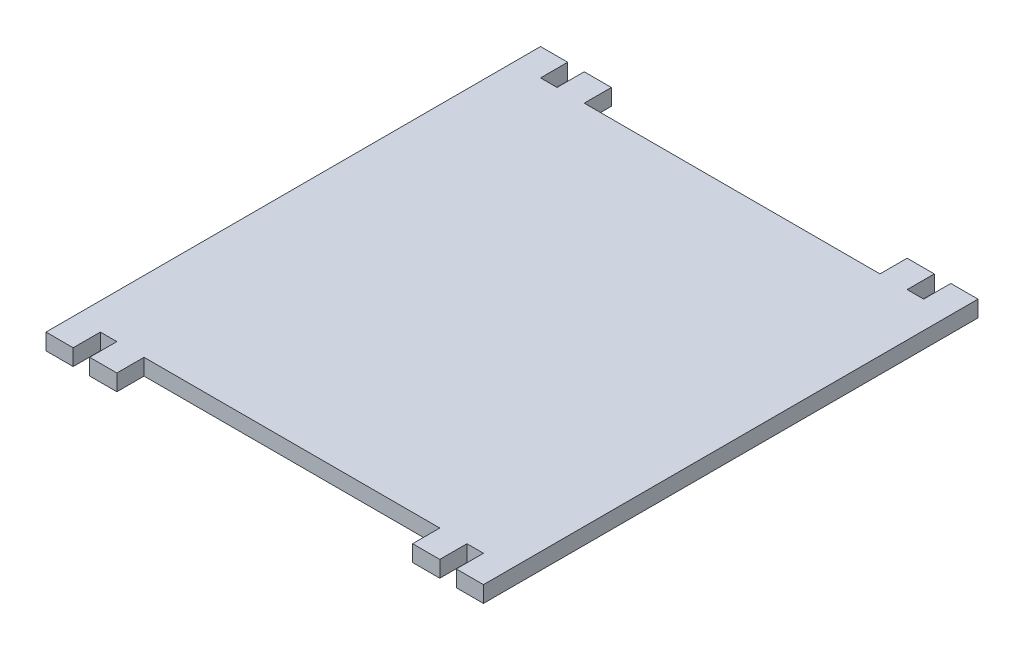
SolidWorks part; units mm, degrees
ref_plane "Front Plane" through (0, 0, 0) normal (0, 0, 1) x (1, 0, 0)
ref_plane "Top Plane" through (0, 0, 0) normal (0, 1, 0) x (1, 0, 0)
ref_plane "Right Plane" through (0, 0, 0) normal (1, 0, 0) x (0, 0, -1)
sketch "Sketch1" plane through (0, 0, 0) normal (0, 1, 0) x (1, 0, 0)
  line L1 (0, 0) -> (70.5, 0)
  line L2 (0, 0) -> (0, -81)
  line L3 (0, -81) -> (70.5, -81)
  line L4 (70.5, 0) -> (70.5, -81)
  dimension "D1" = 70.5
  dimension "D2" = 81
extrude "Boss-Extrude1" add sketch "Sketch1" along normal blind 3
sketch "Sketch2" plane through (0, 0, 81) normal (0, 0, 1) x (1, 0, 0)
  line L0 (0, 3) -> (70.5, 3) construction
  line L1 (3.04, 3) -> (8.04, 3)
  line L2 (3.04, 3) -> (3.04, 0)
  line L3 (3.04, 0) -> (8.04, 0)
  line L4 (8.04, 3) -> (8.04, 0)
  line L5 (0, 0) -> (70.5, 0) construction
  line L6 (70.5, 3) -> (70.5, 0) construction
  line L7 (67.46, 3) -> (62.46, 3)
  line L8 (67.46, 3) -> (67.46, 0)
  line L9 (67.46, 0) -> (62.46, 0)
  line L10 (62.46, 3) -> (62.46, 0)
  line L11 (0, 3) -> (0, 0) construction
  dimension "D1" = 3.04
  dimension "D2" = 5
  dimension "D3" = 5
  dimension "D4" = 3.04
extrude "Boss-Extrude2" add sketch "Sketch2" along normal blind 5
sketch "Sketch3" plane through (0, 0, 0) normal (0, 0, -1) x (-1, 0, 0)
  line L1 (-3.04, 3) -> (-8.04, 3)
  line L2 (-3.04, 3) -> (-3.04, 0)
  line L3 (-3.04, 0) -> (-8.04, 0)
  line L4 (-8.04, 3) -> (-8.04, 0)
  line L5 (-62.46, 3) -> (-67.46, 3)
  line L6 (-62.46, 3) -> (-62.46, 0)
  line L7 (-62.46, 0) -> (-67.46, 0)
  line L8 (-67.46, 3) -> (-67.46, 0)
extrude "Boss-Extrude3" add sketch "Sketch3" along normal blind 5
sketch "Sketch4" plane through (0, 3, 0) normal (0, 1, 0) x (1, 0, 0)
  line L0 (3.04, 5) -> (-4.3072, 5) construction
  line L1 (-4.3072, 5) -> (80.2002, 5) construction
  line L2 (67.46, -86) -> (-4.3072, -86) construction
  line L3 (-4.3072, -86) -> (77.1992, -86) construction
  line L4 (0, 0) -> (0, -81) construction
  line L5 (0, 5) -> (-5, 5)
  line L6 (0, 5) -> (0, -86)
  line L7 (0, -86) -> (-5, -86)
  line L8 (-5, 5) -> (-5, -86)
  line L10 (70.5, 0) -> (70.5, 5)
  line L11 (70.5, 5) -> (75.5, 5)
  line L12 (75.5, 0) -> (75.5, 5)
  line L13 (75.5, 5) -> (70.5, 5)
  line L14 (75.5, 5) -> (75.5, -86)
  line L15 (75.5, -86) -> (70.5, -86)
  line L16 (70.5, 5) -> (70.5, -86)
  line M9 (0, 0) -> (0, -81)
  line M19 (70.5, -81) -> (70.5, 0)
  dimension "D1" = 5
  dimension "D2" = 5
extrude "Boss-Extrude4" add sketch "Sketch4" against normal blind 3 contours L5 L8 L7 L6 M9 | L16 L15 L14 L12 L11 L10 M19
